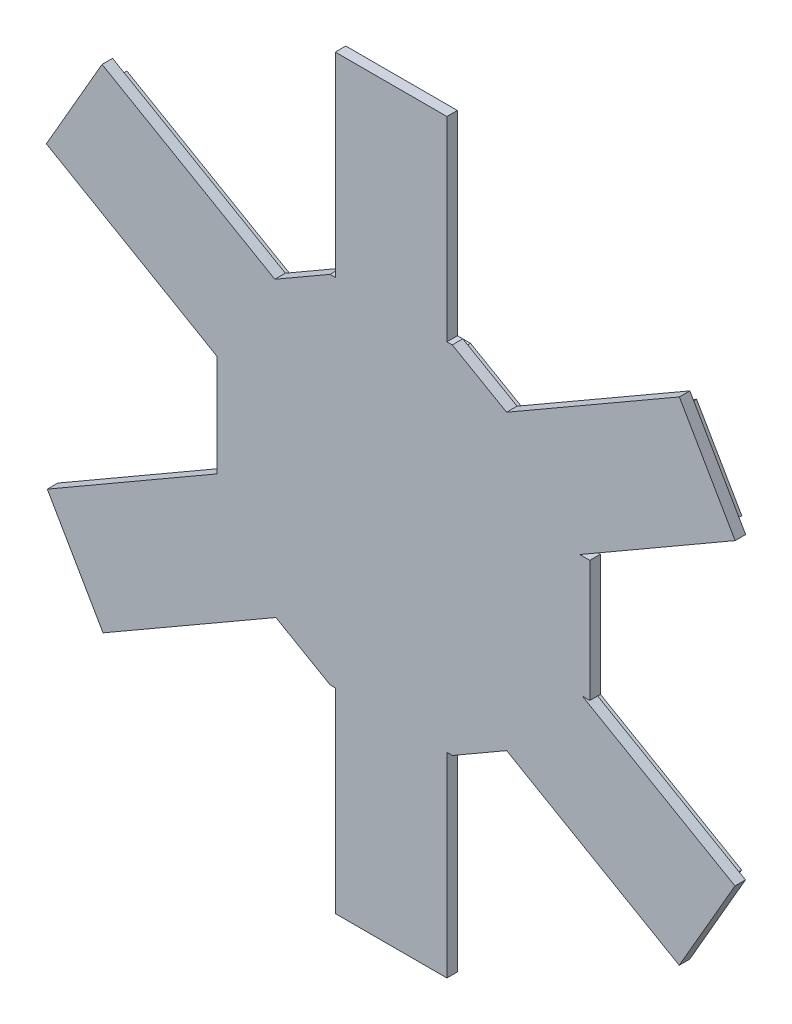
SolidWorks part; units mm, degrees
ref_plane "Ebene vorne" through (0, 0, 0) normal (0, 0, 1) x (1, 0, 0)
ref_plane "Ebene oben" through (0, 0, 0) normal (0, 1, 0) x (1, 0, 0)
ref_plane "Ebene rechts" through (0, 0, 0) normal (1, 0, 0) x (0, 0, -1)
sketch "Skizze1" plane through (0, 0, 14.5885) normal (0, 0, 1) x (1, 0, 0)
  line L30 (-22.1499, 27.7653) -> (-55.0236, 46.7321)
  line L31 (-55.0236, 46.7321) -> (-65.6194, 28.349)
  line L32 (-65.6194, 28.349) -> (-33.18, 9.5827)
  line L33 (-33.18, 9.5827) -> (-33.18, -9.8219)
  line L34 (-33.18, -9.8219) -> (-65.4412, -28.4584)
  line L35 (-65.4412, -28.4584) -> (-54.8327, -46.8414)
  line L36 (-54.8327, -46.8414) -> (-21.9453, -27.8694)
  line L37 (-21.9453, -27.8694) -> (-11.6352, -33.81)
  line L38 (-11.6352, -33.81) -> (-10.63, -33.81)
  line L39 (-10.63, -33.81) -> (-10.63, -71)
  line L40 (-10.63, -71) -> (10.5888, -71)
  line L41 (10.5888, -71) -> (10.6088, -33.81)
  line L42 (10.6088, -33.81) -> (11.6362, -33.81)
  line L43 (11.6362, -33.81) -> (21.9615, -27.8493)
  line L44 (21.9615, -27.8493) -> (54.7917, -46.8016)
  line L45 (54.7917, -46.8016) -> (65.4021, -28.4282)
  line L46 (65.4021, -28.4282) -> (36.3727, -11.67)
  line L47 (36.3727, -11.67) -> (37.79, -11.67)
  line L48 (37.79, -11.67) -> (37.79, 11.42)
  line L49 (37.79, 11.42) -> (35.8755, 11.42)
  line L50 (35.8755, 11.42) -> (65.4319, 28.4885)
  line L51 (65.4319, 28.4885) -> (54.8223, 46.8607)
  line L52 (54.8223, 46.8607) -> (21.9469, 27.9032)
  line L53 (21.9469, 27.9032) -> (11.6127, 33.83)
  line L54 (11.6127, 33.83) -> (10.59, 33.83)
  line L55 (10.59, 33.83) -> (10.59, 70.95)
  line L56 (10.59, 70.95) -> (-10.65, 70.95)
  line L57 (-10.65, 70.95) -> (-10.65, 33.83)
  line L58 (-10.65, 33.83) -> (-11.6358, 33.83)
  line L59 (-11.6358, 33.83) -> (-22.1499, 27.7653)
  line L60 (-22.1499, 27.7653) -> (-55.0236, 46.7321)
  line L61 (-55.0236, 46.7321) -> (-65.6194, 28.349)
  line L62 (-65.6194, 28.349) -> (-33.18, 9.5827)
  line L63 (-33.18, 9.5827) -> (-33.18, -9.8219)
  line L64 (-33.18, -9.8219) -> (-65.4412, -28.4584)
  line L65 (-65.4412, -28.4584) -> (-54.8327, -46.8414)
  line L66 (-54.8327, -46.8414) -> (-21.9453, -27.8694)
  line L67 (-21.9453, -27.8694) -> (-11.6352, -33.81)
  line L68 (-11.6352, -33.81) -> (-10.63, -33.81)
  line L69 (-10.63, -33.81) -> (-10.63, -71)
  line L70 (-10.63, -71) -> (10.5888, -71)
  line L71 (10.5888, -71) -> (10.6088, -33.81)
  line L72 (10.6088, -33.81) -> (11.6362, -33.81)
  line L73 (11.6362, -33.81) -> (21.9615, -27.8493)
  line L74 (21.9615, -27.8493) -> (54.7917, -46.8016)
  line L75 (54.7917, -46.8016) -> (65.4021, -28.4282)
  line L76 (65.4021, -28.4282) -> (36.3727, -11.67)
  line L77 (36.3727, -11.67) -> (37.79, -11.67)
  line L78 (37.79, -11.67) -> (37.79, 11.42)
  line L79 (37.79, 11.42) -> (35.8755, 11.42)
  line L80 (35.8755, 11.42) -> (65.4319, 28.4885)
  line L81 (65.4319, 28.4885) -> (54.8223, 46.8607)
  line L82 (54.8223, 46.8607) -> (21.9469, 27.9032)
  line L83 (21.9469, 27.9032) -> (11.6127, 33.83)
  line L84 (11.6127, 33.83) -> (10.59, 33.83)
  line L85 (10.59, 33.83) -> (10.59, 70.95)
  line L86 (10.59, 70.95) -> (-10.65, 70.95)
  line L87 (-10.65, 70.95) -> (-10.65, 33.83)
  line L88 (-10.65, 33.83) -> (-11.6358, 33.83)
  line L89 (-11.6358, 33.83) -> (-22.1499, 27.7653)
  dimension "D1" = 0
extrude "Aufsatz-Linear austragen1" add sketch "Skizze1" along normal blind 2
sketch "Skizze2" plane through (0, 0, 14.5885) normal (0, 0, -1) x (-1, 0, 0)
  line L0 (29.58, 9.8106) -> (29.58, -10.052)
  line L30 (-28.9078, -9.67) -> (-11.4129, -9.67)
  line L31 (-11.4129, -9.67) -> (-11.4129, 9.42)
  line L32 (-11.4129, 9.42) -> (-28.4129, 9.42)
  line L60 (22.15, 25.4563) -> (11.1003, 31.83)
  line L61 (11.1003, 31.83) -> (8.65, 31.83)
  line L62 (8.65, 31.83) -> (8.65, 68.95)
  line L63 (8.65, 68.95) -> (-8.59, 68.95)
  line L64 (-8.59, 68.95) -> (-8.59, 31.83)
  line L65 (-8.59, 31.83) -> (-11.0799, 31.83)
  line L66 (-11.0799, 31.83) -> (-21.9496, 25.5961)
  line L67 (-21.9496, 25.5961) -> (-54.0899, 44.1297)
  line L68 (-54.0899, 44.1297) -> (-62.6998, 29.2202)
  line L69 (-62.6998, 29.2202) -> (-28.4129, 9.42)
  line L70 (-28.4129, 9.42) -> (-35.79, 9.42)
  line L71 (-35.79, 9.42) -> (-35.79, -9.67)
  line L72 (-35.79, -9.67) -> (-28.9078, -9.67)
  line L73 (-28.9078, -9.67) -> (-62.6698, -29.1602)
  line L74 (-62.6698, -29.1602) -> (-54.0598, -44.0698)
  line L75 (-54.0598, -44.0698) -> (-21.9614, -25.54)
  line L76 (-21.9614, -25.54) -> (-11.1004, -31.81)
  line L77 (-11.1004, -31.81) -> (-8.6098, -31.81)
  line L78 (-8.6098, -31.81) -> (-8.5898, -69)
  line L79 (-8.5898, -69) -> (8.63, -69)
  line L80 (8.63, -69) -> (8.63, -31.81)
  line L81 (8.63, -31.81) -> (11.1002, -31.81)
  line L82 (11.1002, -31.81) -> (21.9459, -25.5609)
  line L83 (21.9459, -25.5609) -> (54.0999, -44.1097)
  line L84 (54.0999, -44.1097) -> (62.7097, -29.1902)
  line L85 (62.7097, -29.1902) -> (31.18, -10.9763)
  line L86 (31.18, -10.9763) -> (31.18, 10.7362)
  line L87 (31.18, 10.7362) -> (62.8895, 29.0803)
  line L88 (62.8895, 29.0803) -> (54.29, 43.9998)
  line L89 (54.29, 43.9998) -> (22.15, 25.4563)
  line L90 (22.15, 25.4563) -> (11.1003, 31.83)
  line L91 (11.1003, 31.83) -> (8.65, 31.83)
  line L92 (8.65, 31.83) -> (8.65, 68.95)
  line L93 (8.65, 68.95) -> (-8.59, 68.95)
  line L94 (-8.59, 68.95) -> (-8.59, 31.83)
  line L95 (-8.59, 31.83) -> (-11.0799, 31.83)
  line L96 (-11.0799, 31.83) -> (-21.9496, 25.5961)
  line L97 (-21.9496, 25.5961) -> (-54.0899, 44.1297)
  line L98 (-54.0899, 44.1297) -> (-62.6998, 29.2202)
  line L99 (-62.6998, 29.2202) -> (-28.4129, 9.42)
  line L100 (-28.4129, 9.42) -> (-35.79, 9.42) construction
  line L101 (-35.79, 9.42) -> (-35.79, -9.67) construction
  line L102 (-35.79, -9.67) -> (-28.9078, -9.67) construction
  line L103 (-28.9078, -9.67) -> (-62.6698, -29.1602)
  line L104 (-62.6698, -29.1602) -> (-54.0598, -44.0698)
  line L105 (-54.0598, -44.0698) -> (-21.9614, -25.54)
  line L106 (-21.9614, -25.54) -> (-11.1004, -31.81)
  line L107 (-11.1004, -31.81) -> (-8.6098, -31.81)
  line L108 (-8.6098, -31.81) -> (-8.5898, -69)
  line L109 (-8.5898, -69) -> (8.63, -69)
  line L110 (8.63, -69) -> (8.63, -31.81)
  line L111 (8.63, -31.81) -> (11.1002, -31.81)
  line L112 (11.1002, -31.81) -> (21.9459, -25.5609)
  line L113 (21.9459, -25.5609) -> (54.0999, -44.1097)
  line L114 (54.0999, -44.1097) -> (62.7097, -29.1902)
  line L115 (62.7097, -29.1902) -> (29.58, -10.052)
  line L116 (31.18, -10.9763) -> (31.18, 10.7362) construction
  line L117 (29.58, 9.8106) -> (62.8895, 29.0803)
  line L118 (62.8895, 29.0803) -> (54.29, 43.9998)
  line L119 (54.29, 43.9998) -> (22.15, 25.4563)
  dimension "D2" = 1.6
  dimension "D3" = 17
  dimension "D1" = 2
extrude "Aufsatz-Linear austragen2" add sketch "Skizze2" along normal blind 2
